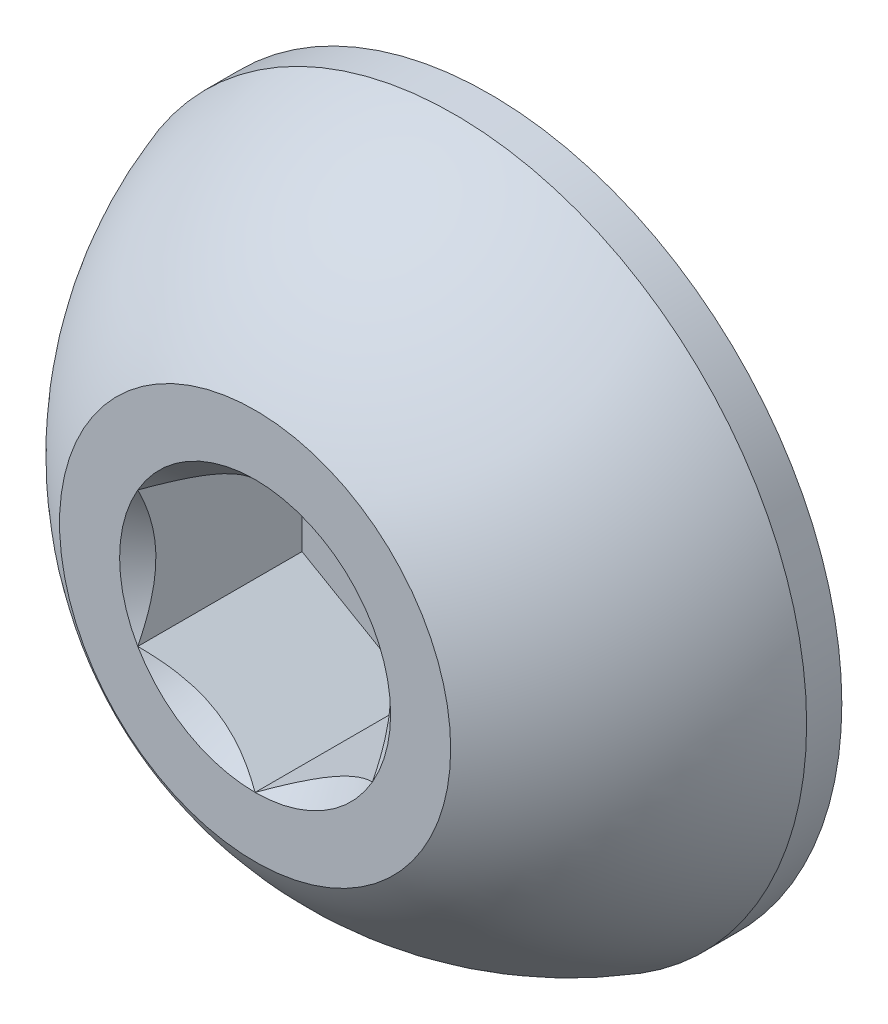
SolidWorks part; units mm, degrees
material "Stainless Steel (ferritic)"
ref_plane "Front" through (0, 0, 0) normal (0, 0, 1) x (1, 0, 0)
ref_plane "Top" through (0, 0, 0) normal (0, 1, 0) x (1, 0, 0)
ref_plane "Right" through (0, 0, 0) normal (1, 0, 0) x (0, 0, -1)
sketch "Sketch1" plane through (0, 0, 0) normal (1, 0, 0) x (0, 0, -1)
  line L2 (1.5, 1.25) -> (5.5, 1.25)
  line L3 (5.5, 1.25) -> (5.5, 0)
  line L4 (5.5, 0) -> (1.5, 0)
  line L6 (1.275, 2.25) -> (1.5, 2.25) construction
  line L7 (5.5, 1.25) -> (5.5, -1.25) construction
  line L8 (0, 0) -> (1.5, 0) construction
  line L9 (1.5, 2.25) -> (1.5, -2.25) construction
  line L11 (1.5, 1.25) -> (1.5, 0)
  line L13 (0, 0.75) -> (0, -0.75) construction
  line L14 (0, 0.75) -> (0, 1.25) construction
  line L15 (5.4719, 1.2987) -> (5.6969, 0.909) construction
  line L16 (5.6969, 0.909) -> (5.9219, 1.2987) construction
  line L17 (5.9219, 1.2987) -> (5.4719, 1.2987) construction
  line L18 (5.5, 1.25) -> (5.8938, 1.25) construction
  line L19 (5.6969, 1.2987) -> (5.6969, 1.25) construction
  line L20 (5.6969, 1.25) -> (5.6969, 0.9577) construction
  line L21 (5.6969, 0.9577) -> (5.6969, 0.909) construction
  line L22 (5.6688, 0.9577) -> (5.725, 0.9577)
  line L23 (5.4859, 1.2744) -> (5.9078, 1.2744)
  line L24 (5.725, 0.9577) -> (5.9078, 1.2744)
  line L25 (5.6688, 0.9577) -> (5.4859, 1.2744)
  line L26 (5.1625, 1.25) -> (5.5, 0.9125)
  arc A3 (0, 1.25) -> (1.275, 2.25) centre (2.01, 0) cw construction
  point P29 (5.6969, 1.2744)
  point P30 (4.375, -1.25)
  dimension "D1" = 0.225
  dimension "Pitch" = 0.45
  dimension "D3" = 0.0563
  dimension "D2" = 0.3375
  dimension "D4" = 45
  dimension "D5" = 1.125
sketch "Sketch7" plane through (0, 0, 0) normal (1, 0, 0) x (0, 0, -1)
  line L6 (1.275, 2.25) -> (1.5, 2.25) construction
  line L8 (0, 0) -> (1.5, 0) construction
  line L11 (1.5, 2.25) -> (1.5, -2.25) construction
  line L12 (1.275, 2.25) -> (1.5, 2.25)
  line L13 (0, 0) -> (1.5, 0)
  line L14 (0, 0.75) -> (0, -0.75) construction
  line L15 (1.5, 2.25) -> (1.5, 0)
  line L16 (0, 1.25) -> (0, 0)
  arc A2 (1.275, 2.25) -> (0, 1.25) centre (2.01, 0) ccw construction
  arc A3 (1.275, 2.25) -> (0, 1.25) centre (2.01, 0) ccw
revolve "Revolve2" add sketch "Sketch7" angle 360 mid plane about L13
sketch "Sketch5" plane through (0, 0, 0) normal (0, 0, 1) x (1, 0, 0)
  line L1 (0.75, -0.433) -> (0.75, 0.433)
  line L2 (0.75, 0.433) -> (0, 0.866)
  line L3 (0, 0.866) -> (-0.75, 0.433)
  line L4 (-0.75, 0.433) -> (-0.75, -0.433)
  line L5 (-0.75, -0.433) -> (0, -0.866)
  line L6 (0, -0.866) -> (0.75, -0.433)
  circle A0 centre (0, 0) radius 0.75 construction
extrude "Cut-Extrude2" cut sketch "Sketch5" against normal blind 1.05
sketch "Sketch6" plane through (0, 0, 0) normal (0, 0, 1) x (1, 0, 0)
  circle A0 centre (0, 0) radius 0.866
extrude "Cut-Extrude3" cut sketch "Sketch6" against normal blind 1.05 draft 45
equation "\"D1@Cut-Extrude2\" = \"Head Ht@Sketch1\" * .7"
equation "\"D1@Sketch1\" = \"Head Ht@Sketch1\" * .15"
equation "\"D1@Cut-Extrude3\" = \"D1@Cut-Extrude2\""
equation "\"D3@Sketch1\" = \"Pitch@Sketch1\" / 8"
equation "\"D2@Sketch1\"=\"Pitch@Sketch1\"*0.75"
equation "\"D5@Sketch1\"=\"Pitch@Sketch1\"*2.5"
